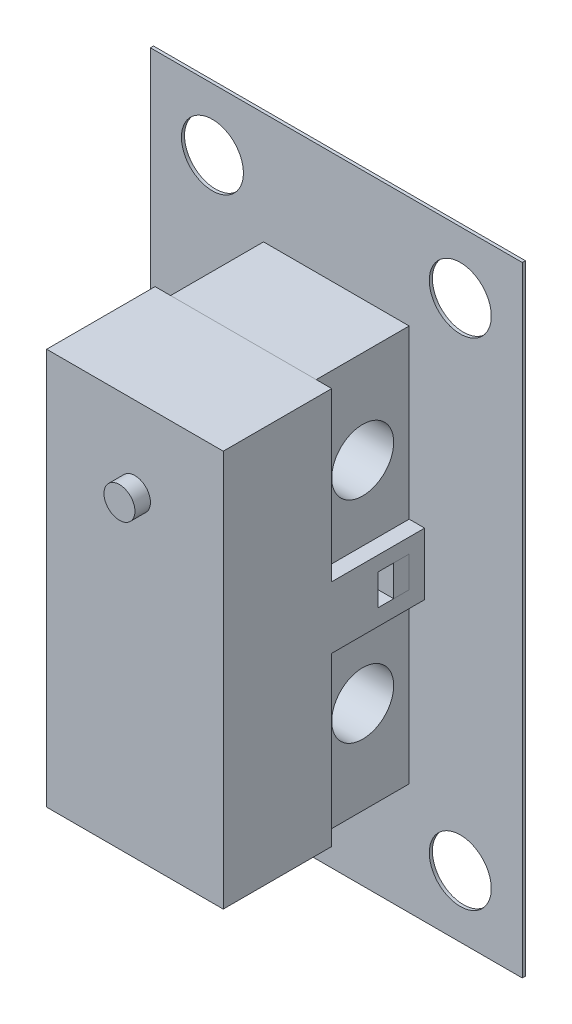
SolidWorks part; units mm, degrees
material "Plástico personalizado"
ref_plane "Alzado" through (0, 0, 0) normal (0, 0, 1) x (1, 0, 0)
ref_plane "Planta" through (0, 0, 0) normal (0, 1, 0) x (1, 0, 0)
ref_plane "Vista lateral" through (0, 0, 0) normal (1, 0, 0) x (0, 0, -1)
sketch "Sketch1" plane through (0, 0, 0) normal (0, 0, 1) x (1, 0, 0)
  line L1 (1.9718, 19.0836) -> (7.6718, 19.0836)
  line L2 (1.9718, 19.0836) -> (1.9718, 6.2836)
  line L3 (1.9718, 6.2836) -> (7.6718, 6.2836)
  line L4 (7.6718, 19.0836) -> (7.6718, 6.2836)
  dimension "D1" = 5.7
  dimension "D2" = 12.8
extrude "Boss-Extrude2" add sketch "Sketch1" along normal blind 6.5
sketch "Sketch3" plane through (0, 0, 6.5) normal (0, 0, 1) x (1, 0, 0)
  circle A0 centre (4.8218, 16.6018) radius 0.575
extrude "Boss-Extrude3" add sketch "Sketch3" along normal blind 0.5
sketch "Sketch7" plane through (7.6718, 0, 0) normal (1, 0, 0) x (0, 0, -1)
  line L0 (-6.5, 6.2836) -> (0, 6.2836) construction
  line L1 (0, 19.0836) -> (-3, 19.0836)
  line L2 (0, 19.0836) -> (0, 6.2836)
  line L3 (0, 6.2836) -> (-3, 6.2836)
  line L4 (-3, 19.0836) -> (-3, 6.2836)
  dimension "D1" = 3
extrude "Cut-Extrude1" cut sketch "Sketch7" against normal blind 0.5
sketch "Sketch8" plane through (1.9718, 0, 0) normal (-1, 0, 0) x (0, 0, 1)
  line L0 (6.5, 19.0836) -> (0, 19.0836) construction
  line L1 (0, 6.2836) -> (3, 6.2836)
  line L2 (0, 6.2836) -> (0, 19.0836)
  line L3 (0, 19.0836) -> (3, 19.0836)
  line L4 (3, 6.2836) -> (3, 19.0836)
  dimension "D1" = 3
extrude "Cut-Extrude2" cut sketch "Sketch8" against normal blind 0.5
sketch "Sketch9" plane through (7.1718, 0, 0) normal (1, 0, 0) x (0, 0, -1)
  line L0 (-3, 6.2836) -> (0, 6.2836) construction
  line L1 (0, 19.0836) -> (-3, 19.0836) construction
  circle A0 centre (-1.6614, 9.7836) radius 1
  circle A1 centre (-1.6614, 15.5836) radius 1
  dimension "D1" = 2
  dimension "D2" = 3.5
  dimension "D3" = 3.5
extrude "Cut-Extrude3" cut sketch "Sketch9" against normal through all
sketch "Sketch10" plane through (1.9718, 0, 0) normal (-1, 0, 0) x (0, 0, 1)
  line L0 (0, 12.6836) -> (6.5, 12.6836) construction
  line L1 (0, 19.0836) -> (0, 6.2836) construction
  line L2 (6.5, 19.0836) -> (6.5, 6.2836) construction
  line L3 (3, 6.2836) -> (3, 19.0836) construction
  line L4 (6, 11.6836) -> (0, 11.6836)
  line L5 (6, 11.6836) -> (6, 13.6836)
  line L6 (6, 13.6836) -> (0, 13.6836)
  line L7 (0, 11.6836) -> (0, 13.6836)
  line L8 (6, 11.6836) -> (0, 13.6836) construction
  line L9 (6, 13.6836) -> (0, 11.6836) construction
  point P6 (3, 12.6836)
  dimension "D1" = 2
extrude "Boss-Extrude4" add sketch "Sketch10" against normal blind 0.5
sketch "Sketch11" plane through (7.6718, 0, 0) normal (1, 0, 0) x (0, 0, -1)
  line L0 (-6.5, 12.6836) -> (0, 12.6836) construction
  line L1 (-6.5, 6.2836) -> (-6.5, 19.0836) construction
  line L2 (0, 6.2836) -> (0, 19.0836) construction
  line L3 (-3, 19.0836) -> (-3, 6.2836) construction
  line L4 (-6, 13.6836) -> (0, 13.6836)
  line L5 (-6, 13.6836) -> (-6, 11.6836)
  line L6 (-6, 11.6836) -> (0, 11.6836)
  line L7 (0, 13.6836) -> (0, 11.6836)
  line L8 (-6, 13.6836) -> (0, 11.6836) construction
  line L9 (-6, 11.6836) -> (0, 13.6836) construction
  point P6 (-3, 12.6836)
  dimension "D1" = 2
extrude "Boss-Extrude6" add sketch "Sketch11" against normal blind 0.5
sketch "Sketch13" plane through (0, 19.0836, 0) normal (0, 1, 0) x (1, 0, 0)
  line L1 (7.1718, -3) -> (2.4718, -3)
  line L2 (7.1718, -3) -> (7.1718, 0)
  line L3 (7.1718, 0) -> (2.4718, 0)
  line L4 (2.4718, -3) -> (2.4718, 0)
extrude "Cut-Extrude4" cut sketch "Sketch13" against normal through all
sketch "Sketch16" plane through (0, 19.0836, 0) normal (0, 1, 0) x (1, 0, 0)
  line L1 (2.4718, -3) -> (7.1718, -3)
  line L2 (2.4718, -3) -> (2.4718, 0)
  line L3 (2.4718, 0) -> (7.1718, 0)
  line L4 (7.1718, -3) -> (7.1718, 0)
extrude "Boss-Extrude8" add sketch "Sketch16" against normal blind 12.8 separate body
sketch "Sketch17" plane through (7.1718, 0, 0) normal (1, 0, 0) x (0, 0, -1)
  line L0 (-3, 19.0836) -> (0, 19.0836) construction
  line L1 (-3, 6.2836) -> (0, 6.2836) construction
  line L3 (0, 6.2836) -> (0, 19.0836) construction
  circle A0 centre (-1.5, 16.0836) radius 1
  circle A1 centre (-1.5, 9.2836) radius 1
  dimension "D1" = 3
  dimension "D2" = 3
  dimension "D3" = 1.5
extrude "Cut-Extrude5" cut sketch "Sketch17" against normal through all
sketch "Sketch18" plane through (0, 0, 7) normal (0, 0, 1) x (1, 0, 0)
  circle A0 centre (4.8218, 16.6018) radius 0.575
extrude "Cut-Extrude6" cut sketch "Sketch18" against normal up to surface (0.5 mm away) up to face at (5.3968, 16.6018, 6.5)
sketch "Sketch19" plane through (0, 0, 6.5) normal (0, 0, 1) x (1, 0, 0)
  circle A0 centre (4.8218, 16.4768) radius 0.5
extrude "Boss-Extrude9" add sketch "Sketch19" along normal blind 0.5 separate body
sketch "Sketch20" plane through (7.6718, 0, 0) normal (1, 0, 0) x (0, 0, -1)
  line L0 (0, 11.6836) -> (0, 13.6836) construction
  line L1 (-1.5, 13.2098) -> (-0.5, 13.2098)
  line L2 (-1.5, 13.2098) -> (-1.5, 12.2098)
  line L3 (-1.5, 12.2098) -> (-0.5, 12.2098)
  line L4 (-0.5, 13.2098) -> (-0.5, 12.2098)
  line L5 (-1.5, 13.2098) -> (-0.5, 12.2098) construction
  line L6 (-1.5, 12.2098) -> (-0.5, 13.2098) construction
  point P0 (-1, 12.7098)
  dimension "D1" = 1
  dimension "D2" = 1
  dimension "D3" = 0.5
extrude "Cut-Extrude8" cut sketch "Sketch20" against normal blind 0.5
sketch "Sketch21" plane through (7.1718, 0, 0) normal (1, 0, 0) x (0, 0, -1)
  line L0 (-1.5, 12.2098) -> (-0.5, 12.2098) construction
  line L1 (-0.5, 13.2098) -> (-1, 13.2098)
  line L2 (-0.5, 13.2098) -> (-0.5, 12.2098)
  line L3 (-0.5, 12.2098) -> (-1, 12.2098)
  line L4 (-1, 13.2098) -> (-1, 12.2098)
extrude "Boss-Extrude11" add sketch "Sketch21" along normal blind 0.5 separate body
sketch "Sketch22" plane through (1.9718, 0, 0) normal (-1, 0, 0) x (0, 0, 1)
  line L0 (0, 13.6836) -> (0, 11.6836) construction
  line L1 (0.5, 13.1392) -> (1.5, 13.1392)
  line L2 (0.5, 13.1392) -> (0.5, 12.1392)
  line L3 (0.5, 12.1392) -> (1.5, 12.1392)
  line L4 (1.5, 13.1392) -> (1.5, 12.1392)
  line L5 (0.5, 13.1392) -> (1.5, 12.1392) construction
  line L6 (0.5, 12.1392) -> (1.5, 13.1392) construction
  point P0 (1, 12.6392)
  dimension "D1" = 0.5
  dimension "D2" = 1
extrude "Cut-Extrude9" cut sketch "Sketch22" against normal blind 0.5
sketch "Sketch23" plane through (2.4718, 0, 0) normal (-1, 0, 0) x (0, 0, 1)
  line L0 (0.5, 12.1392) -> (1.5, 12.1392) construction
  line L1 (0.5, 13.1392) -> (1, 13.1392)
  line L2 (0.5, 13.1392) -> (0.5, 12.1392)
  line L3 (0.5, 12.1392) -> (1, 12.1392)
  line L4 (1, 13.1392) -> (1, 12.1392)
extrude "Boss-Extrude13" add sketch "Sketch23" along normal blind 0.5 separate body
sketch "Sketch28" plane through (0, 0, 0) normal (0, 0, -1) x (-1, 0, 0)
  line L0 (-7.1718, 19.0836) -> (-2.4718, 19.0836) construction
  line L1 (-10.8218, 22.6836) -> (1.1782, 22.6836)
  line L2 (-10.8218, 22.6836) -> (-10.8218, 2.6836)
  line L3 (-10.8218, 2.6836) -> (1.1782, 2.6836)
  line L4 (1.1782, 22.6836) -> (1.1782, 2.6836)
  line L5 (-7.1718, 6.2836) -> (-7.1718, 19.0836) construction
  point P6 (-4.8218, 19.0836)
  point P10 (-7.1718, 12.6836)
  dimension "D1" = 12
  dimension "D2" = 20
  dimension "D3" = 6
  dimension "D4" = 10
extrude "Boss-Extrude15" add sketch "Sketch28" along normal blind 0.1 separate body
sketch "Sketch29" plane through (0, 0, -0.1) normal (0, 0, -1) x (-1, 0, 0)
  line L0 (1.1782, 22.6836) -> (-10.8218, 22.6836) construction
  line L1 (-10.8218, 22.6836) -> (-10.8218, 2.6836) construction
  line L2 (-10.8218, 2.6836) -> (1.1782, 2.6836) construction
  line L3 (1.1782, 2.6836) -> (1.1782, 22.6836) construction
  circle A0 centre (-8.8218, 20.6836) radius 1
  circle A1 centre (-8.8218, 4.6836) radius 1
  circle A2 centre (-0.8218, 4.6836) radius 1
  circle A3 centre (-0.8218, 20.6836) radius 1
  dimension "D1" = 2
  dimension "D3" = 2
  dimension "D4" = 2
  dimension "D2" = 2
extrude "Cut-Extrude10" cut sketch "Sketch29" against normal blind 10.1
